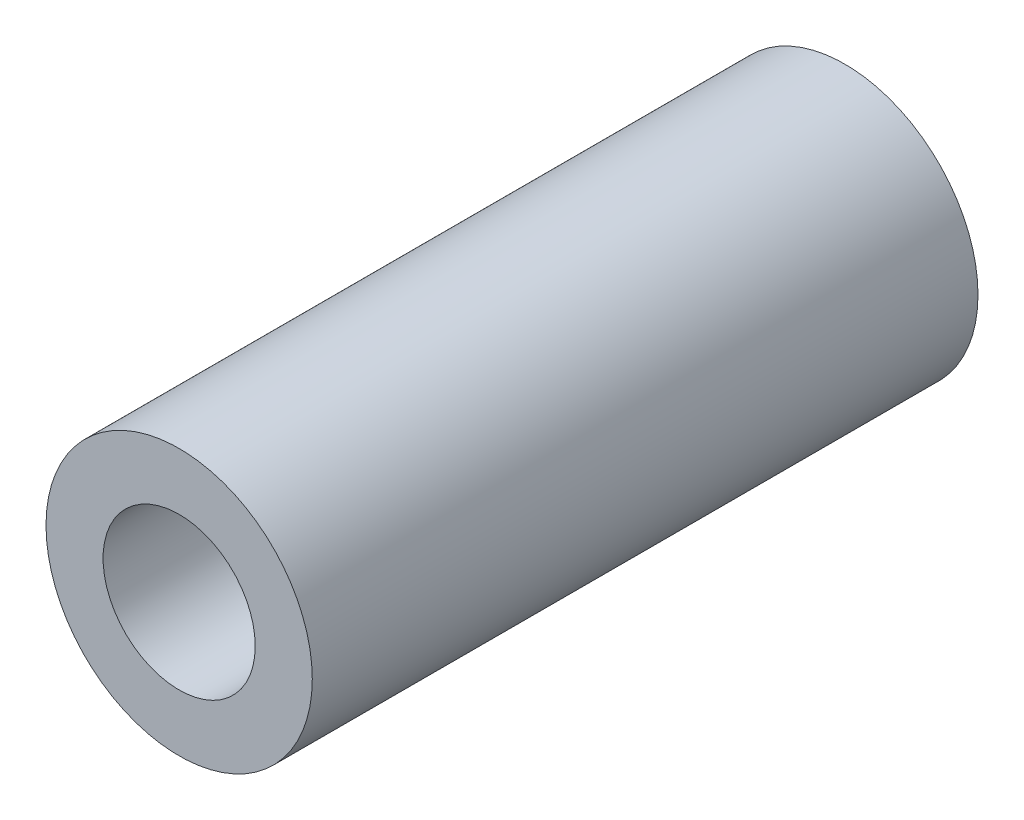
SolidWorks part; units mm, degrees
ref_plane "Front Plane" through (0, 0, 0) normal (0, 0, 1) x (1, 0, 0)
ref_plane "Top Plane" through (0, 0, 0) normal (0, 1, 0) x (1, 0, 0)
ref_plane "Right Plane" through (0, 0, 0) normal (1, 0, 0) x (0, 0, -1)
sketch "Sketch1" plane through (0, 0, 0) normal (0, 0, 1) x (1, 0, 0)
  circle A0 centre (0, 0) radius 7
  circle A2 centre (0, 0) radius 4
extrude "Boss-Extrude1" add sketch "Sketch1" along normal blind 35
